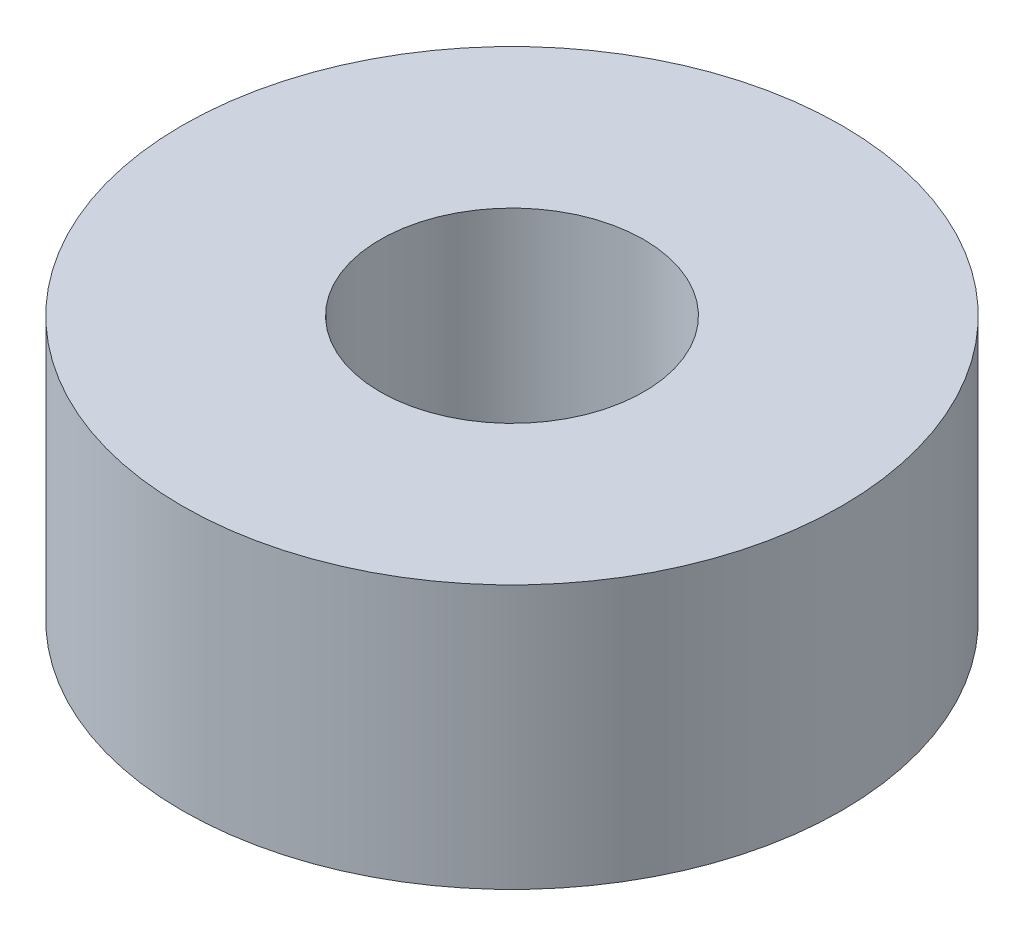
SolidWorks part; units mm, degrees
ref_plane "Front Plane" through (0, 0, 0) normal (0, 0, 1) x (1, 0, 0)
ref_plane "Top Plane" through (0, 0, 0) normal (0, 1, 0) x (1, 0, 0)
ref_plane "Right Plane" through (0, 0, 0) normal (1, 0, 0) x (0, 0, -1)
sketch "Sketch1" plane through (0, 0, 0) normal (0, 1, 0) x (1, 0, 0)
  circle A0 centre (0, 0) radius 2.5
  circle A1 centre (0, 0) radius 1
  dimension "D1" = 5
  dimension "D2" = 2
extrude "Boss-Extrude1" add sketch "Sketch1" along normal blind 2
